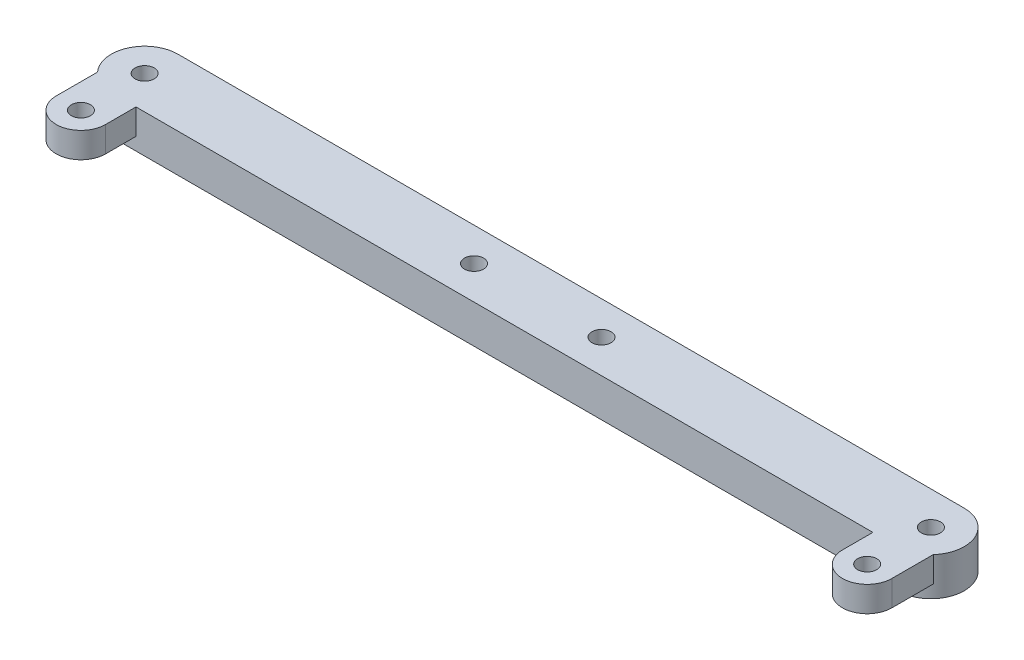
SolidWorks part; units mm, degrees
ref_plane "Front Plane" through (0, 0, 0) normal (0, 0, 1) x (1, 0, 0)
ref_plane "Top Plane" through (0, 0, 0) normal (0, 1, 0) x (1, 0, 0)
ref_plane "Right Plane" through (0, 0, 0) normal (1, 0, 0) x (0, 0, -1)
sketch "Sketch1" plane through (0, 0, 0) normal (0, 1, 0) x (1, 0, 0)
  line L0 (0, 0) -> (123.36, 0) construction
  line L1 (0, 0) -> (123.36, 0) construction
  line L2 (0, 5.2306) -> (123.36, 5.2306)
  line L3 (0, -5.2306) -> (123.36, -5.2306)
  circle A0 centre (0, 0) radius 1.5
  circle A1 centre (123.36, 0) radius 1.5
  arc A2 (0, 5.2306) -> (0, -5.2306) centre (0, 0) ccw
  arc A3 (123.36, -5.2306) -> (123.36, 5.2306) centre (123.36, 0) ccw
  point P5 (61.68, 0)
  dimension "D1" = 123.36
extrude "Boss-Extrude1" add sketch "Sketch1" along normal blind 6 contours A0 | A1 | L3 A3 L2 A2
sketch "Sketch2" plane through (0, 6, 0) normal (0, 1, 0) x (1, 0, 0)
  line L0 (0, 0) -> (0, -10) construction
  line L1 (0, 0) -> (0, -10) construction
  line L2 (3.8766, 0) -> (3.8766, -10)
  line L3 (-3.8766, 0) -> (-3.8766, -10)
  line L4 (0, 0) -> (123.36, 0) construction
  line L5 (61.68, 0) -> (61.68, 14.0841) construction
  line L6 (123.36, 0) -> (123.36, -10) construction
  line L7 (119.4834, 0) -> (119.4834, -10)
  line L8 (127.2366, 0) -> (127.2366, -10)
  circle A0 centre (0, -10) radius 1.5
  arc A1 (3.8766, 0) -> (-3.8766, 0) centre (0, 0) ccw
  arc A2 (-3.8766, -10) -> (3.8766, -10) centre (0, -10) ccw
  circle A3 centre (0, 0) radius 1.5
  circle A4 centre (123.36, 0) radius 1.5
  circle A5 centre (123.36, -10) radius 1.5
  arc A6 (119.4834, 0) -> (127.2366, 0) centre (123.36, 0) cw
  arc A7 (127.2366, -10) -> (119.4834, -10) centre (123.36, -10) cw
  point P4 (0, -5)
  point P19 (123.36, -5)
  circle M7 centre (0, 0) radius 1.5
  line M9 (0, -5.2306) -> (123.36, -5.2306)
  arc M10 (123.36, -5.2306) -> (123.36, 5.2306) centre (123.36, 0) ccw
  circle M12 centre (123.36, 0) radius 1.5
  dimension "D1" = 10
extrude "Boss-Extrude2" add sketch "Sketch2" against normal blind 4 contours A7 L8 L7 A5 M10 M9 | A6 L7 L8 M9 M10 M12 | A0 | M7 | L3 A2 L2 A1 | A3
sketch "Sketch3" plane through (0, 6, 0) normal (0, 1, 0) x (1, 0, 0)
  line L0 (61.68, 5.2306) -> (61.68, -5.2306) construction
  line L1 (0, 5.2306) -> (123.36, 5.2306) construction
  line L2 (3.8766, -5.2306) -> (119.4834, -5.2306) construction
  line L3 (61.68, 0) -> (51.68, 0) construction
  line L4 (61.68, 0) -> (71.68, 0) construction
  circle A0 centre (51.68, 0) radius 1.5
  circle A1 centre (71.68, 0) radius 1.5
  dimension "D1" = 10
  dimension "D2" = 10
extrude "Cut-Extrude1" cut sketch "Sketch3" against normal blind 10
